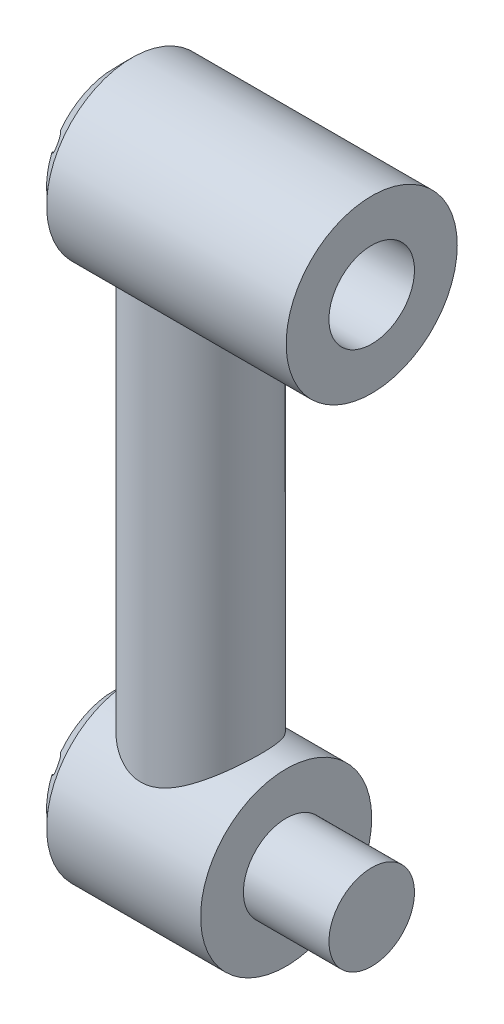
SolidWorks part; units mm, degrees
ref_plane "Front Plane" through (0, 0, 0) normal (0, 0, 1) x (1, 0, 0)
ref_plane "Top Plane" through (0, 0, 0) normal (0, 1, 0) x (1, 0, 0)
ref_plane "Right Plane" through (0, 0, 0) normal (1, 0, 0) x (0, 0, -1)
sketch "Sketch1" plane through (0, 0, 0) normal (0, 1, 0) x (1, 0, 0)
  circle A0 centre (0, 0) radius 88.9
  dimension "D1" = 177.8
extrude "Boss-Extrude1" add sketch "Sketch1" along normal mid plane 635
sketch "Sketch4" plane through (0, 0, 0) normal (1, 0, 0) x (0, 0, -1)
  line L0 (0, 317.5) -> (0, 495.3)
  line L1 (88.9, 317.5) -> (-88.9, 317.5) construction
  line L2 (0, -317.5) -> (0, -469.9)
  line L3 (-88.9, -317.5) -> (88.9, -317.5) construction
  circle A0 centre (0, 406.4) radius 127
  circle A1 centre (0, -393.7) radius 127
  dimension "D2" = 254
  dimension "D4" = 254
  dimension "D1" = 177.8
  dimension "D3" = 152.4
extrude "Boss-Extrude2" add sketch "Sketch4" along normal mid plane 254
sketch "Sketch5" plane through (127, 0, 0) normal (1, 0, 0) x (0, 0, -1)
  circle A0 centre (0, -393.7) radius 63.5
  circle A1 centre (0, -393.7) radius 127 construction
  dimension "D2" = 127
  dimension "D1" = 63.5
extrude "Boss-Extrude3" add sketch "Sketch5" along normal blind 127
sketch "Sketch6" plane through (127, 0, 0) normal (1, 0, 0) x (0, 0, -1)
  circle A0 centre (0, 406.4) radius 63.5
  circle A1 centre (0, 406.4) radius 127
  circle A2 centre (0, 406.4) radius 127
  dimension "D2" = 127
  dimension "D1" = 0
extrude "Boss-Extrude4" add sketch "Sketch6" along normal blind 127
chamfer "Chamfer1" distance 25.4 angle 45 2 edges at (-127, -393.7, -127) (-127, 406.4, -127)
sketch "Sketch7" plane through (-127, 0, 0) normal (-1, 0, 0) x (0, 0, 1)
  circle A0 centre (0, 508) radius 12.7
  circle A1 centre (0, 406.4) radius 101.6 construction
  circle A2 centre (0, -292.1) radius 12.7
  circle A3 centre (0, -393.7) radius 101.6 construction
  circle A4 centre (87.9882, 457.2) radius 12.7
  circle A5 centre (87.9882, 355.6) radius 12.7
  circle A6 centre (0, 304.8) radius 12.7
  circle A7 centre (-87.9882, 355.6) radius 12.7
  circle A8 centre (-87.9882, 457.2) radius 12.7
  circle A9 centre (87.9882, -342.9) radius 12.7
  circle A10 centre (87.9882, -444.5) radius 12.7
  circle A11 centre (0, -495.3) radius 12.7
  circle A12 centre (-87.9882, -444.5) radius 12.7
  circle A13 centre (-87.9882, -342.9) radius 12.7
  point P21 (0, 406.4)
  point P31 (0, -393.7)
  dimension "D1" = 25.4
  dimension "D2" = 25.4
  dimension "D3" = 6
  dimension "D4" = 6
extrude "Cut-Extrude1" cut sketch "Sketch7" against normal blind 25.4
